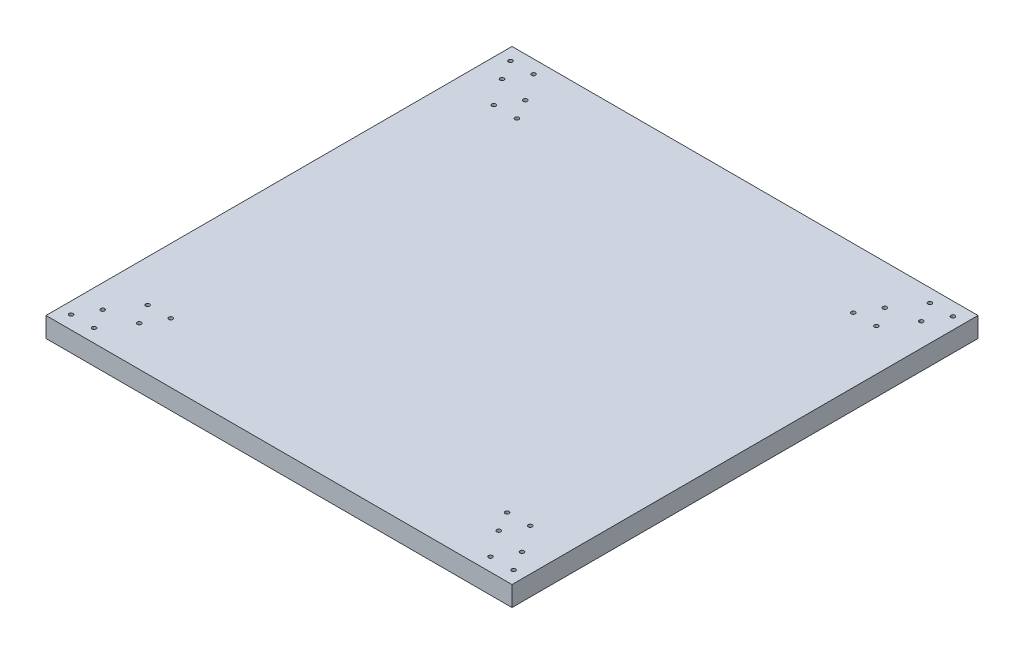
SolidWorks part; units mm, degrees
ref_plane "Front Plane" through (0, 0, 0) normal (0, 0, 1) x (1, 0, 0)
ref_plane "Top Plane" through (0, 0, 0) normal (0, 1, 0) x (1, 0, 0)
ref_plane "Right Plane" through (0, 0, 0) normal (1, 0, 0) x (0, 0, -1)
sketch "Sketch2" plane through (0, 0, 0) normal (0, 1, 0) x (1, 0, 0)
  line L1 (-172.6542, 106.5013) -> (177.3458, 106.5013)
  line L2 (-172.6542, 106.5013) -> (-172.6542, -243.4987)
  line L3 (-172.6542, -243.4987) -> (177.3458, -243.4987)
  line L4 (177.3458, 106.5013) -> (177.3458, -243.4987)
  circle A1 centre (159.8458, -218.4987) radius 1.5
  circle A2 centre (168.5061, -233.4987) radius 1.5
  circle A3 centre (151.1856, -233.4987) radius 1.5
  circle A4 centre (168.5061, 96.5013) radius 1.5
  circle A5 centre (159.8458, 81.5013) radius 1.5
  circle A6 centre (151.1856, 96.5013) radius 1.5
  circle A7 centre (-163.8144, 96.5013) radius 1.5
  circle A8 centre (-146.4939, 96.5013) radius 1.5
  circle A9 centre (-155.1542, 81.5013) radius 1.5
  circle A10 centre (-155.1542, -218.4987) radius 1.5
  circle A11 centre (-146.4939, -233.4987) radius 1.5
  circle A12 centre (-163.8144, -233.4987) radius 1.5
  circle A15 centre (137.3458, 76.5013) radius 1.5
  circle A19 centre (146.0061, 61.5013) radius 1.5
  circle A20 centre (128.6856, 61.5013) radius 1.5
  circle A21 centre (-123.9939, 61.5013) radius 1.5
  circle A22 centre (-141.3144, 61.5013) radius 1.5
  circle A23 centre (-132.6542, 76.5013) radius 1.5
  circle A24 centre (-141.3144, -198.4987) radius 1.5
  circle A25 centre (-123.9939, -198.4987) radius 1.5
  circle A26 centre (-132.6542, -213.4987) radius 1.5
  circle A27 centre (128.6856, -198.4987) radius 1.5
  circle A28 centre (146.0061, -198.4987) radius 1.5
  circle A29 centre (137.3458, -213.4987) radius 1.5
  point P52 (0, 0)
  dimension "D3" = 3
  dimension "D5" = 270
  dimension "D1" = 350
  dimension "D2" = 350
  dimension "D7" = 260
  dimension "D4" = 3
  dimension "D6" = 3
extrude "Boss-Extrude1" add sketch "Sketch2" along normal blind 15
